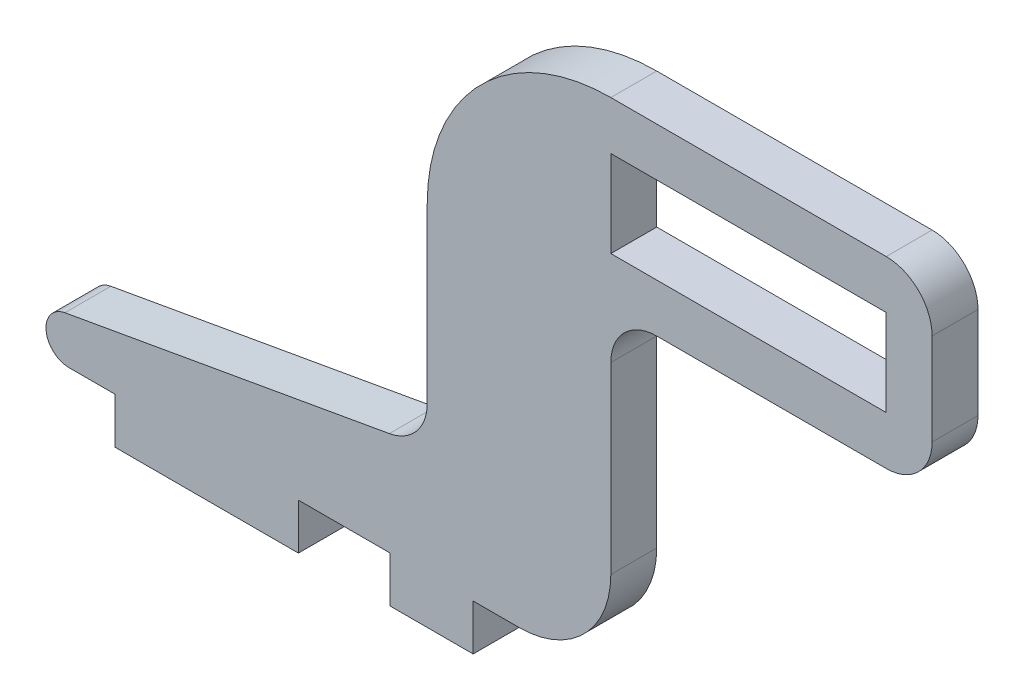
SolidWorks part; units mm, degrees
ref_plane "Front Plane" through (0, 0, 0) normal (0, 0, 1) x (1, 0, 0)
ref_plane "Top Plane" through (0, 0, 0) normal (0, 1, 0) x (1, 0, 0)
ref_plane "Right Plane" through (0, 0, 0) normal (1, 0, 0) x (0, 0, -1)
sketch "Sketch1" plane through (0, 0, 0) normal (0, 0, 1) x (1, 0, 0)
  line L0 (0, 3.175) -> (6.35, 3.175)
  line L1 (0, 0) -> (-12.7, 0)
  line L2 (0, 0) -> (0, 3.175)
  line L3 (-12.7, 3.175) -> (-15.875, 3.175)
  line L4 (-12.7, 0) -> (-12.7, 3.175)
  line L5 (15.2622, 3.175) -> (15.2622, 15.875) construction
  line L6 (6.35, 3.175) -> (6.35, 0)
  line L7 (6.35, 0) -> (12.0872, 0)
  line L8 (12.0872, 3.175) -> (12.0872, 0)
  line L9 (12.0872, 3.175) -> (15.2622, 3.175)
  line L10 (8.9122, 10.7721) -> (-16.1523, 6.3256)
  line L11 (12.0872, 3.175) -> (-12.7, 3.175) construction
  line L12 (21.6122, 9.525) -> (21.6122, 25.4)
  line L13 (8.9122, 10.7721) -> (8.9122, 25.4)
  line L14 (21.6122, 25.4) -> (43.8372, 25.4)
  line L15 (8.9122, 9.525) -> (8.9122, 25.4) construction
  line L16 (43.8372, 38.1) -> (21.6122, 38.1)
  line L17 (43.8372, 31.75) -> (10.6137, 31.75) construction
  line L18 (43.8372, 38.1) -> (43.8372, 25.4) construction
  line L19 (40.6622, 28.7528) -> (21.6122, 28.7528)
  line L20 (40.6622, 28.7528) -> (40.6622, 34.7472)
  line L21 (40.6622, 34.7472) -> (21.6122, 34.7472)
  line L22 (21.6122, 28.7528) -> (21.6122, 34.7472)
  line L23 (31.1372, 34.7472) -> (31.1372, 28.7528) construction
  line L24 (40.6622, 31.75) -> (21.6122, 31.75) construction
  line L25 (43.8372, 25.4) -> (43.8372, 38.1)
  arc A0 (-16.1523, 6.3256) -> (-15.875, 3.175) centre (-15.875, 4.7625) ccw
  arc A1 (15.2622, 3.175) -> (21.6122, 9.525) centre (15.2622, 9.525) ccw
  arc A4 (21.6122, 38.1) -> (8.9122, 25.4) centre (21.6122, 25.4) ccw
  point P26 (31.1372, 31.75)
  dimension "D6" = 3.175
  dimension "D10" = 22.225
  dimension "D11" = 19.05
  dimension "D1" = 12.7
  dimension "D2" = 3.175
  dimension "D3" = 6.35
  dimension "D4" = 3.175
  dimension "D5" = 3.175
  dimension "D7" = 12.7
  dimension "D8" = 15.875
  dimension "D12" = 5.9944
  dimension "D13" = 0
  dimension "D9" = 12.7
extrude "Boss-Extrude1" add sketch "Sketch1" along normal blind 3.175
fillet "Fillet1" radius 3.175 2 edges at (21.6122, 25.4, 1.5875) (8.9122, 10.7721, 1.5875)
fillet "Fillet2" radius 3.175 2 edges at (43.8372, 38.1, 1.5875) (43.8372, 25.4, 1.5875)
